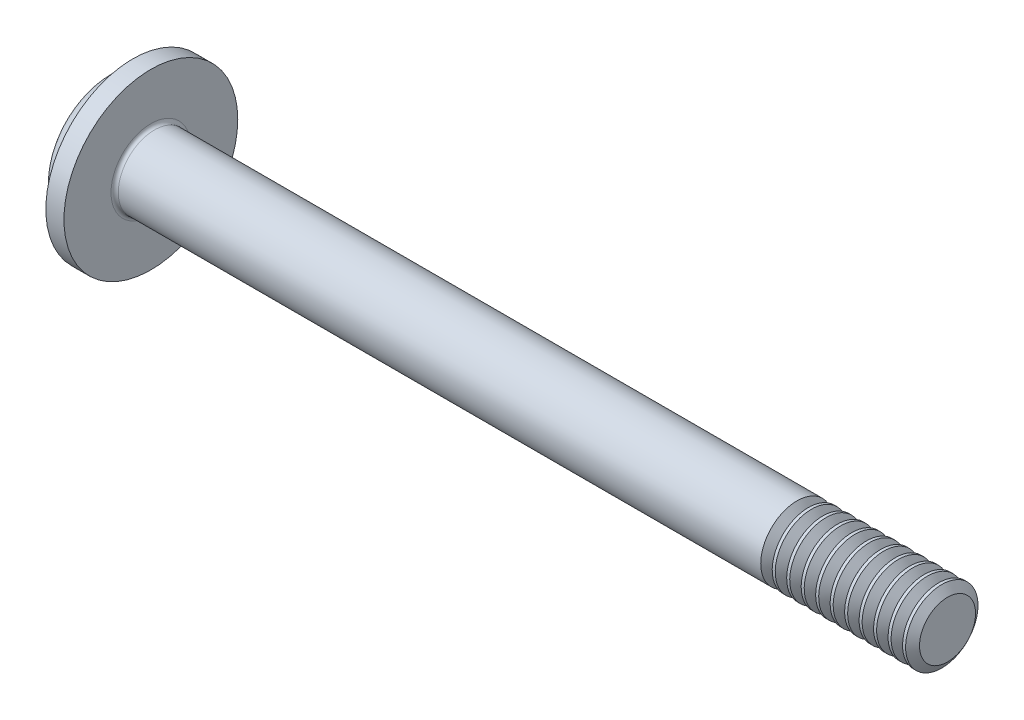
SolidWorks part; units mm, degrees
material "Aço NB 1045"
ref_plane "Plane1" through (0, 0, 0) normal (0, 0, 1) x (1, 0, 0)
ref_plane "Plane2" through (0, 0, 0) normal (0, 1, 0) x (1, 0, 0)
ref_plane "Plane3" through (0, 0, 0) normal (1, 0, 0) x (0, 0, -1)
sketch "BodySke" plane through (0, 0, 0) normal (0, 0, 1) x (1, 0, 0)
  line L0 (1.6, 1) -> (1.6, 2)
  line L1 (1.8, 6.35) -> (1.8, -3.175) construction
  line L2 (-25.4, 0) -> (127, 0) construction
  line L3 (23.6, 0) -> (0, 0)
  line L4 (1.6, 1) -> (23.6, 1)
  line L5 (23.6, 1) -> (23.6, 0)
  line L6 (1.1, 2) -> (1.6, 2)
  line L8 (19.6, 6.35) -> (19.6, -3.175) construction
  arc A0 (0.3941, 1.5765) -> (0, 0) centre (3.35, 0) ccw
  arc A2 (0.3941, 1.5765) -> (1.1, 2) centre (1.1, 1.2) cw
  dimension "D2" = 0.8
  dimension "Length" = 22
  dimension "Head_ht" = 1.6
  dimension "Head_dia" = 4
  dimension "Advance" = 0.4
  dimension "Thread_nom" = 4
  dimension "Diameter" = 2
  dimension "D1" = 0.5
revolve "Base-Revolve" add sketch "BodySke"
cosmetic thread "ThreadCosmetic" [suppressed]
fillet "Fillet1" radius 0.1 1 edges at (1.6, 0, 1)
sketch "Sketch3" plane through (0, 0, 0) normal (1, 0, 0) x (0, 0, -1)
  line L0 (0.24, -1.05) -> (-0.24, -1.05)
  line L1 (0.24, -1.05) -> (0.24, 1.05)
  line L2 (-0.24, 1.05) -> (0.24, 1.05)
  line L3 (-0.24, 1.05) -> (-0.24, -1.05)
  dimension "Cross_dia" = 2.1
  dimension "D1" = 1.05
  dimension "Cross_width" = 0.48
  dimension "D2" = 0.24
ref_plane "Plane4" through (1.42, 0, 0) normal (1, 0, 0) x (0, 0, -1)
sketch "Sketch4" plane through (1.42, 0, 0) normal (1, 0, 0) x (0, 0, -1)
  line L0 (0.24, -0.342) -> (-0.24, -0.342)
  line L1 (0.24, -0.342) -> (0.24, 0.342)
  line L2 (-0.24, 0.342) -> (0.24, 0.342)
  line L3 (-0.24, 0.342) -> (-0.24, -0.342)
  dimension "D1" = 0.48
  dimension "D2" = 0.684
  dimension "D3" = 0.24
  dimension "D4" = 0.342
loft "Recess" cut profiles "Sketch3", "Sketch4"
pattern_circular "RecPat" count 2 every 90 about axis through (0, 0, 0) along (1, 0, 0) of "Recess"
sketch "RecCorSke" plane through (0, 0, 0) normal (0, 0, 1) x (1, 0, 0)
  line L0 (-3.175, 0) -> (15.875, 0) construction
  line L1 (-25.4, 0) -> (127, 0) construction
  line L2 (0, 0) -> (0, 0.4548)
  line L3 (0, 0.4548) -> (1.42, 0.3555)
  line L4 (1.42, 0.3555) -> (1.5355, 0)
  line L5 (1.5355, 0) -> (0, 0)
  dimension "Diameter" = 0.711
  dimension "Depth" = 1.42
  dimension "Draft_angle" = 4
  dimension "Bottom_angle" = 18
revolve "RecessCore" cut sketch "RecCorSke" angle 360 about L0
sketch "ThdSchSke" plane through (0, 0, 0) normal (0, 0, 1) x (1, 0, 0)
  line L0 (19.6, -0.774) -> (19.4418, -1)
  line L1 (19.6, -0.774) -> (19.7582, -1)
  line L2 (19.7582, -1) -> (19.7582, -1.25)
  line L3 (-3.175, 0) -> (5.1513, 0) construction
  line L5 (19.7582, -1.25) -> (19.4418, -1.25)
  line L6 (19.4418, -1.25) -> (19.4418, -1)
  dimension "Diameter" = 2
  dimension "SideAngle" = 55
  dimension "VeeAngle" = 70
  dimension "Thread_minor" = 1.548
  dimension "Overcut" = 2.5
  dimension "Start" = 19.6
revolve "ThreadSchematic" cut sketch "ThdSchSke" angle 360 about L3
pattern_linear "ThdSchPat" count 11 spacing 0.4 along (1, 0, 0) of "ThreadSchematic"
sketch "Esboço1" plane through (1.6, 0, 0) normal (1, 0, 0) x (0, 0, -1)
  circle A0 centre (0, 0) radius 2.4
  dimension "D1" = 4.8
extrude "Ressalto-extrusão1" add sketch "Esboço1" against normal blind 0.5
sketch "Esboço2" plane through (0, 0, 0) normal (0, 1, 0) x (1, 0, 0)
  line L0 (0, 0) -> (9.6, 0) construction
  line L1 (9.6, -0.774) -> (9.6, 0.774) construction
  line L2 (9.6, 0.3) -> (8.1, 1)
  line L4 (8.1, 1) -> (9.6, 1)
  line L5 (9.6, 1) -> (9.6, 0.3)
  line L6 (7.5813, 1) -> (7.5024, 1) construction
  dimension "D1" = 1.5
  dimension "D2" = 0.6
equation "\"D1@Sketch3\" = \"Cross_dia@Sketch3\" / 2"
equation "\"D2@Sketch3\" = \"Cross_width@Sketch3\" / 2"
equation "\"Depth@RecCorSke\" = \"Cross_depth@Plane4\""
equation "\"D1@Sketch4\" = \"Cross_width@Sketch3\""
equation "\"D2@Sketch4\" = \"Cross_dia@Sketch3\" - 2.0 * \"Cross_depth@Plane4\" * tan(26.5  * 0.017453292)"
equation "\"D3@Sketch4\" = \"D1@Sketch4\" / 2"
equation "\"D4@Sketch4\" = \"D2@Sketch4\" / 2"
equation "\"Thread_length@ThreadCosmetic\" = ((sgn( (\"Length@BodySke\" - \"Advance@BodySke\" * 2.0 ) - \"Thread_nom@BodySke\" )-1)*( (\"Length@BodySke\" - \"Advance@BodySke\" * 2.0 ) - \"Thread_nom@BodySke\" ))/-2+ \"Thread_nom@BodySke\""
equation "\"Thread_minor@ThdSchSke\" = \"Thread_minor@ThreadCosmetic\""
equation "\"Diameter@ThdSchSke\" = \"Diameter@BodySke\""
equation "\"Overcut@ThdSchSke\" = \"Diameter@BodySke\" * 1.25"
equation "\"Start@ThdSchSke\" = \"Head_ht@BodySke\" + \"Length@BodySke\" - \"Thread_length@ThreadCosmetic\"  '---Non-countersunk---"
equation "\"Num_threads@ThdSchPat\" = int( \"Thread_length@ThreadCosmetic\" / \"Advance@BodySke\" + 0.999 )  + 1"
equation "\"Advance@ThdSchPat\" = \"Thread_length@ThreadCosmetic\" /  (\"Num_threads@ThdSchPat\" - 1) 'relax it"
